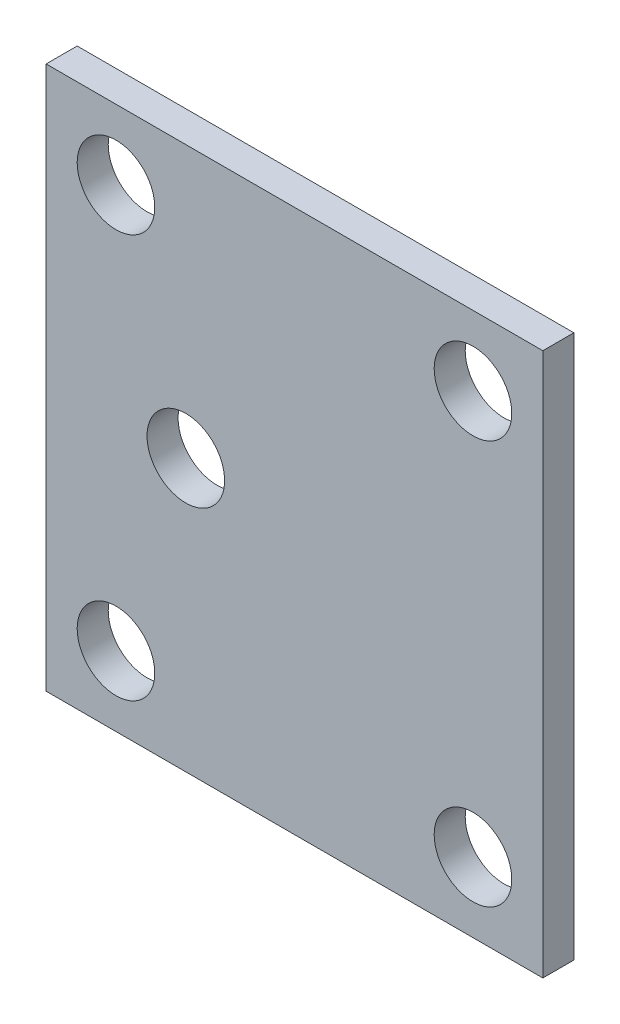
SolidWorks part; units mm, degrees
ref_plane "Front Plane" through (0, 0, 0) normal (0, 0, 1) x (1, 0, 0)
ref_plane "Top Plane" through (0, 0, 0) normal (0, 1, 0) x (1, 0, 0)
ref_plane "Right Plane" through (0, 0, 0) normal (1, 0, 0) x (0, 0, -1)
sketch "Sketch1" plane through (0, 0, 0) normal (0, 0, 1) x (1, 0, 0)
  line L1 (-14.33, 12.25) -> (17.67, 12.25)
  line L2 (-14.33, 12.25) -> (-14.33, -22.75)
  line L3 (-14.33, -22.75) -> (17.67, -22.75)
  line L4 (17.67, 12.25) -> (17.67, -22.75)
  dimension "D1" = 32
  dimension "D2" = 35
extrude "Boss-Extrude1" add sketch "Sketch1" along normal blind 2
sketch "Sketch3" plane through (0, 0, 0) normal (0, 0, -1) x (-1, 0, 0)
  line L0 (14.33, 12.25) -> (14.33, -22.75) construction
  line L1 (-17.67, 12.25) -> (14.33, 12.25) construction
  line L2 (14.33, -22.75) -> (-17.67, -22.75) construction
  line L3 (14.33, 12.25) -> (14.33, -22.75) construction
  line L4 (-17.67, -22.75) -> (-17.67, 12.25) construction
  circle A0 centre (9.83, 7.75) radius 3
  circle A1 centre (9.83, -18.25) radius 3
  circle A2 centre (-13.17, -18.25) radius 3
  circle A3 centre (-13.17, 7.75) radius 3
  dimension "D1" = 6
  dimension "D2" = 4.5
  dimension "D3" = 4.5
  dimension "D4" = 4.5
  dimension "D5" = 4.5
  dimension "D6" = 4.5
  dimension "D7" = 4.5
  dimension "D8" = 4.5
  dimension "D9" = 4.5
hole_wizard "M6 Tapped Hole3" positions "Sketch7" profile "Sketch8" tap size "M6" standard "KS" end condition through all
sketch "Sketch7" plane through (0, 0, 0) normal (0, 0, -1) x (-1, 0, 0)
  point P0 (9.83, -18.25)
  point P3 (-13.17, -18.25)
  point P6 (-13.17, 7.75)
  point P9 (9.83, 7.75)
sketch "Sketch8" plane through (-9.83, -18.25, 0) normal (1, 0, 0) x (0, 1, 0)
  line L0 (0, 0) -> (0, 2)
  line L1 (0, 2) -> (2.5, 2)
  line L2 (2.5, 2) -> (2.5, 0)
  line L5 (2.5, 0) -> (0, 0)
  line L11 (0, -6.35) -> (0, 107.95) construction
  dimension "Thru Tap Drill Dia." = 5
  dimension "Thru Tap Drill Depth" = 2
cosmetic thread "Hole Thread1" parameters "D2"=6
cosmetic thread "Hole Thread2" parameters "D2"=6
cosmetic thread "Hole Thread3" parameters "D2"=6
cosmetic thread "Hole Thread4" parameters "D2"=6
sketch "Sketch9" plane through (0, 0, 0) normal (0, 0, -1) x (-1, 0, 0)
  circle A0 centre (5.33, -5.25) radius 3
  dimension "D1" = 6
hole_wizard "M6 Tapped Hole4" positions "Sketch10" profile "Sketch11" tap size "M6" standard "DIN" end condition through all
sketch "Sketch10" plane through (0, 0, 0) normal (0, 0, -1) x (-1, 0, 0)
  point P0 (5.33, -5.25)
sketch "Sketch11" plane through (-5.33, -5.25, 0) normal (1, 0, 0) x (0, 1, 0)
  line L0 (0, 0) -> (0, 2)
  line L1 (0, 2) -> (2.5, 2)
  line L2 (2.5, 2) -> (2.5, 0)
  line L5 (2.5, 0) -> (0, 0)
  line L11 (0, -6.35) -> (0, 107.95) construction
  dimension "Thru Tap Drill Dia." = 5
  dimension "Thru Tap Drill Depth" = 2
cosmetic thread "Hole Thread5" parameters "D2"=6
